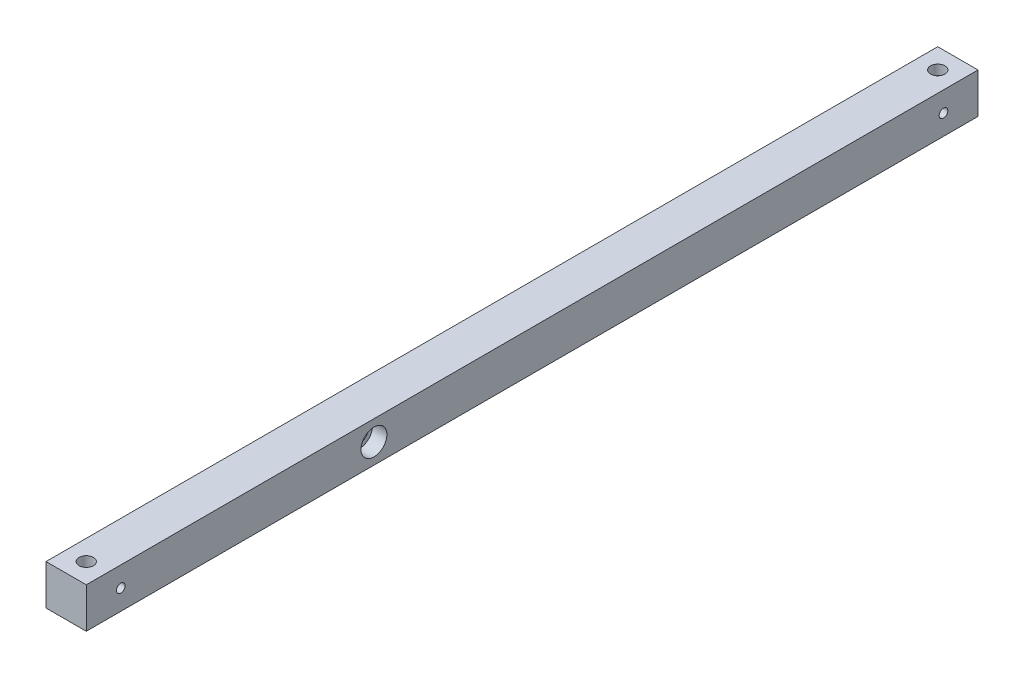
SolidWorks part; units mm, degrees
ref_plane "Ön Düzlem" through (0, 0, 0) normal (0, 0, 1) x (1, 0, 0)
ref_plane "Üst Düzlem" through (0, 0, 0) normal (0, 1, 0) x (1, 0, 0)
ref_plane "Sağ Düzlem" through (0, 0, 0) normal (1, 0, 0) x (0, 0, -1)
sketch "Çizim1" plane through (0, 0, 0) normal (0, 0, 1) x (1, 0, 0)
  line L1 (-14, -14) -> (14, -14)
  line L2 (-14, -14) -> (-14, 14)
  line L3 (-14, 14) -> (14, 14)
  line L4 (14, -14) -> (14, 14)
  line L5 (-14, -14) -> (14, 14) construction
  line L6 (-14, 14) -> (14, -14) construction
  point P0 (0, 0)
  dimension "D1" = 28
  dimension "D2" = 28
extrude "Yükseklik-Ekstrüzyon1" add sketch "Çizim1" along normal blind 620
sketch "Çizim3" plane through (0, 14, 0) normal (0, 1, 0) x (1, 0, 0)
  line L0 (-14, -620) -> (-14, 0) construction
  line L1 (-14, -606.7866) -> (14, -606.7866) construction
  line L2 (14, -620) -> (14, 0) construction
  line L3 (14, -620) -> (-14, -620) construction
  line L4 (14, 0) -> (-14, 0) construction
  circle A0 centre (0, -14) radius 5
  circle A1 centre (0, -606) radius 5
  point P11 (0, -606.7866)
  dimension "D1" = 10
  dimension "D2" = 14
  dimension "D3" = 14
extrude "Kes-Ekstrüzyon2" cut sketch "Çizim3" against normal blind 7
sketch "Çizim4" plane through (0, 14, 0) normal (0, 1, 0) x (1, 0, 0)
  circle A0 centre (0, -606) radius 3
  circle A1 centre (0, -14) radius 3
  dimension "D1" = 6
  dimension "D2" = 6
extrude "Kes-Ekstrüzyon3" cut sketch "Çizim4" against normal through all
sketch "Çizim5" plane through (14, 0, 0) normal (1, 0, 0) x (0, 0, -1)
  line L0 (-557.5222, 14) -> (-557.5222, -14) construction
  line L1 (-620, 14) -> (0, 14) construction
  line L2 (-620, -14) -> (0, -14) construction
  line L3 (-620, -14) -> (-620, 14) construction
  circle A0 centre (-420, 0) radius 6
  point P8 (-557.5222, 0)
  dimension "D1" = 12
  dimension "D2" = 200
extrude "Kes-Ekstrüzyon4" cut sketch "Çizim5" against normal through all
sketch "Çizim6" plane through (14, 0, 0) normal (1, 0, 0) x (0, 0, -1)
  circle A0 centre (-420, 0) radius 9
  dimension "D1" = 18
extrude "Kes-Ekstrüzyon5" cut sketch "Çizim6" against normal blind 10
sketch "Çizim7" plane through (14, 0, 0) normal (1, 0, 0) x (0, 0, -1)
  line L0 (0, -14) -> (0, 14) construction
  line L1 (-620, -14) -> (-620, 14) construction
  circle A0 centre (-24, 0) radius 3
  circle A1 centre (-596, 0) radius 3
  point P4 (0, 0)
  point P6 (0, 0)
  dimension "D1" = 24
  dimension "D3" = 6
  dimension "D2" = 24
extrude "Kes-Ekstrüzyon6" cut sketch "Çizim7" against normal up to next
sketch "Çizim9" plane through (-14, 0, 0) normal (-1, 0, 0) x (0, 0, 1)
  circle A8 centre (596, 0) radius 5
  circle A9 centre (24, 0) radius 5
  dimension "D1" = 10
extrude "Kes-Ekstrüzyon8" cut sketch "Çizim9" against normal blind 7
